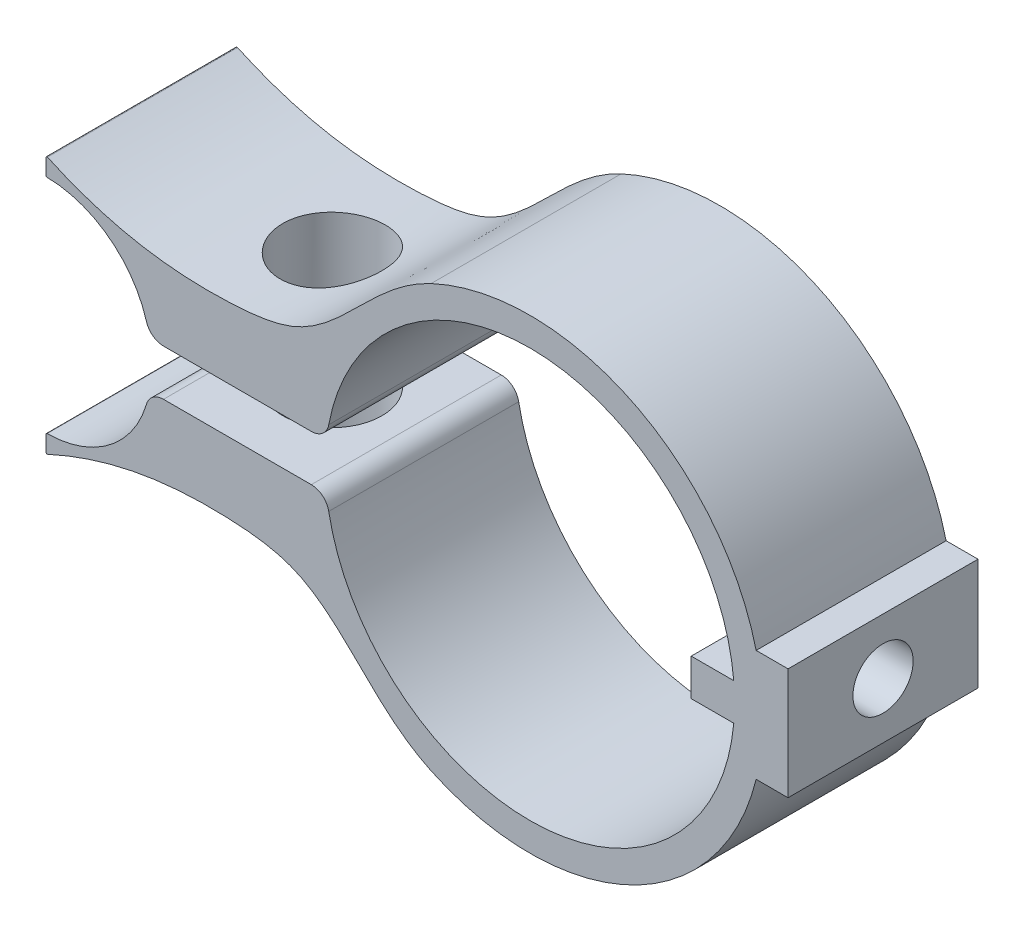
SolidWorks part; units mm, degrees
material "1060 Alloy"
ref_plane "Front Plane" through (0, 0, 0) normal (0, 0, 1) x (1, 0, 0)
ref_plane "Top Plane" through (0, 0, 0) normal (0, 1, 0) x (1, 0, 0)
ref_plane "Right Plane" through (0, 0, 0) normal (1, 0, 0) x (0, 0, -1)
sketch "Sketch1" plane through (0, 0, 0) normal (0, 0, 1) x (1, 0, 0)
  line L0 (-40.1153, 0) -> (32.6644, 0) construction
  line L3 (16.2143, -4.0005) -> (18.5003, -4.0005)
  line L6 (-34.6848, -9.1519) -> (-34.6848, -8.0293)
  line L7 (-26.264, -1.651) -> (-15.6686, -1.651)
  line L8 (18.5003, -4.0005) -> (18.5003, 4.0005)
  line L9 (11.5609, 1.3208) -> (11.5609, -1.3208)
  line L10 (11.5609, -1.3208) -> (14.6089, -1.3208)
  line L11 (11.5609, 1.3208) -> (14.6089, 1.3208)
  line L12 (-26.264, 1.651) -> (-15.6686, 1.651)
  line L13 (-34.6848, 9.1519) -> (-34.6848, 8.0293)
  line L14 (16.2143, 4.0005) -> (18.5003, 4.0005)
  arc A5 (-7.0819, -15.1246) -> (16.2143, -4.0005) centre (0, 0) ccw
  arc A6 (-34.6093, -7.9531) -> (-27.4825, -2.563) centre (-34.6848, -0.4468) ccw
  arc A7 (-14.4201, -2.6883) -> (14.6089, -1.3208) centre (0, 0) ccw
  arc A8 (-27.4825, -2.563) -> (-26.264, -1.651) centre (-26.264, -2.921) cw
  arc A9 (-15.6686, -1.651) -> (-14.4201, -2.6883) centre (-15.6686, -2.921) cw
  arc A10 (-34.6848, -9.1519) -> (-34.5768, -9.2211) centre (-34.6086, -9.1519) ccw
  arc A11 (-34.6093, -7.9531) -> (-34.6848, -8.0293) centre (-34.6086, -8.0293) ccw
  arc A12 (-7.0819, 15.1246) -> (16.2143, 4.0005) centre (0, 0) cw
  arc A13 (-34.6093, 7.9531) -> (-34.6848, 8.0293) centre (-34.6086, 8.0293) cw
  arc A14 (-34.6848, 9.1519) -> (-34.5768, 9.2211) centre (-34.6086, 9.1519) cw
  arc A15 (-15.6686, 1.651) -> (-14.4201, 2.6883) centre (-15.6686, 2.921) ccw
  arc A16 (-27.4825, 2.563) -> (-26.264, 1.651) centre (-26.264, 2.921) ccw
  arc A17 (-14.4201, 2.6883) -> (14.6089, 1.3208) centre (0, 0) cw
  arc A18 (-34.6093, 7.9531) -> (-27.4825, 2.563) centre (-34.6848, 0.4468) cw
  spline S0 degree 3 poles (-34.5768, -9.2211) (-31.2117, -7.6748) (-26.9363, -6.6698) (-21.0373, -6.6806) (-14.0502, -7.4338) (-11.3709, -13.1163) (-7.0819, -15.1246) knots 0.003614 0.003614 0.003614 0.003614 0.34146 0.44633 0.584047 1 1 1 1
  spline S1 degree 3 poles (-34.5768, 9.2211) (-31.2117, 7.6748) (-26.9363, 6.6698) (-21.0373, 6.6806) (-14.0502, 7.4338) (-11.3709, 13.1163) (-7.0819, 15.1246) knots 0.003614 0.003614 0.003614 0.003614 0.34146 0.44633 0.584047 1 1 1 1
  point P3 (-34.6848, -7.9535)
  point P7 (-21.3508, -6.731)
  point P19 (-27.2753, -1.651)
  point P22 (-14.5753, -1.651)
  point P28 (-34.6848, -7.9535)
  point P32 (11.5609, 0)
  point P40 (18.5003, 0)
  point P53 (-34.6848, 7.9535)
  point P54 (-14.5753, 1.651)
  point P55 (-27.2753, 1.651)
  point P56 (-21.3508, 6.731)
  dimension "D1" = 33.401
  dimension "D2" = 0.0762
  dimension "D6" = 1.27
  dimension "D7" = 2.032
  dimension "D8" = 7.5067
  dimension "D9" = 1.27
  dimension "D3" = 3.048
  dimension "D4" = 5.08
  dimension "D5" = 12.7
  dimension "D10" = 4.0005
  dimension "D11" = 2.286
  dimension "D12" = 1.3208
extrude "Boss-Extrude1" add sketch "Sketch1" along normal blind 13.6144
sketch "Sketch2" plane through (18.5003, 0, 0) normal (1, 0, 0) x (0, 0, -1)
  line L0 (-13.6144, 4.0005) -> (0, 4.0005) construction
  circle A0 centre (-6.8072, 0) radius 2.159
  point P6 (-6.8072, 4.0005)
  dimension "D1" = 4.318
extrude "Cut-Extrude1" cut sketch "Sketch2" against normal blind 13.6144
sketch "Sketch3" plane through (0, 1.651, 0) normal (0, -1, 0) x (1, 0, 0)
  line L0 (-15.6686, 13.6144) -> (-15.6686, 0) construction
  line L1 (-15.6686, 0) -> (-26.264, 0) construction
  circle A0 centre (-20.9663, 6.8072) radius 3.556
  point P6 (-15.6686, 6.8072)
  point P9 (-20.9663, 0)
  dimension "D1" = 7.112
extrude "Cut-Extrude2" cut sketch "Sketch3" against normal through all both and the other way through all
